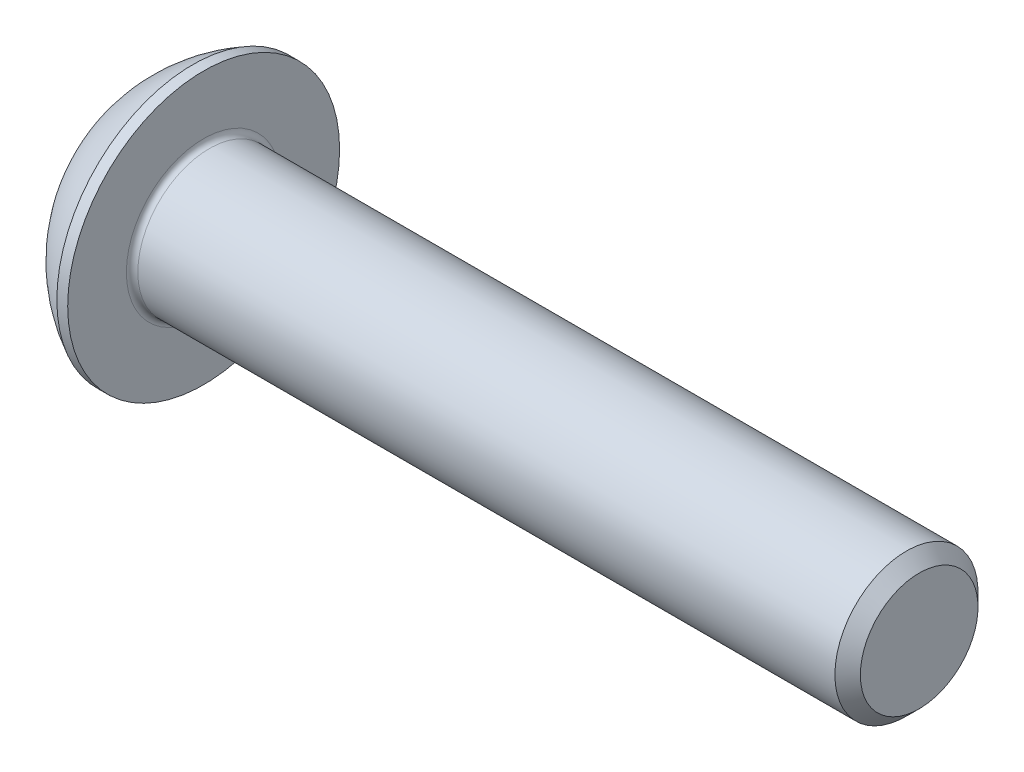
SolidWorks part; units mm, degrees
ref_plane "Plane1" through (0, 0, 0) normal (0, 0, 1) x (1, 0, 0)
ref_plane "Plane2" through (0, 0, 0) normal (0, 1, 0) x (1, 0, 0)
ref_plane "Plane3" through (0, 0, 0) normal (1, 0, 0) x (0, 0, -1)
sketch "BodySke" plane through (0, 0, 0) normal (0, 0, 1) x (1, 0, 0)
  line L0 (27.75, 0) -> (27.75, 2.055)
  line L1 (27.305, 2.5) -> (2.75, 2.5)
  line L2 (2.75, 2.5) -> (2.75, 4.75)
  line L3 (2.75, 4.75) -> (2.37, 4.75)
  line L4 (0, 0) -> (101.6, 0) construction
  line L5 (2.75, -4.75) -> (2.37, -4.75) construction
  line L6 (55.6768, -2.5) -> (2.75, -2.5) construction
  line L7 (27.75, 0) -> (0, 0)
  line L8 (0, 2.375) -> (0, -2.375) construction
  line L9 (0, 0) -> (0, 2.375)
  line L10 (27.75, 2.055) -> (27.305, 2.5)
  line L11 (27.75, -2.055) -> (27.305, -2.5) construction
  line L12 (3.55, 9.525) -> (3.55, -2.5) construction
  line L13 (2.75, 9.525) -> (2.75, -2.5) construction
  arc A1 (0, 2.375) -> (2.37, 4.75) centre (4.755, 0) cw
  dimension "D1" = 4.75
  dimension "Diameter" = 5
  dimension "Length" = 25
  dimension "Head_dia" = 9.5
  dimension "Head_ht" = 2.75
  dimension "Head_side_ht" = 0.38
  dimension "Minor_dia" = 4.11
  dimension "Body_ch_ang" = 45
  dimension "Advance" = 0.8
  dimension "Thread_nom" = 25
revolve "BaseBody" add sketch "BodySke" angle 360 about L4
cosmetic thread "ThreadCosmetic" [suppressed] parameters "Thread_length"=23.4, "Thread_minor"=4.11
fillet "Fillet1" radius 0.2 1 edges at (2.75, 0, 2.5)
sketch "Sketch2" plane through (0, 0, 0) normal (0, 0, 1) x (1, 0, 0)
  line L0 (0, 1.5) -> (1.56, 1.5)
  line L1 (1.56, 1.5) -> (2.426, 0)
  line L3 (2.426, 0) -> (0, 0)
  line L4 (0, 0) -> (0, 1.5)
  line L5 (0, -1.5) -> (1.56, -1.5) construction
  line L6 (0, 0) -> (47.625, 0) construction
  dimension "D2" = 60
  dimension "PreBroach_depth" = 1.56
  dimension "PreBroach_dia" = 3
revolve "PreBroach" cut sketch "Sketch2" angle 360 about L6
sketch "Sketch3" plane through (0, 0, 0) normal (1, 0, 0) x (0, 0, -1)
  line L0 (-1.5, -0.866) -> (-1.5, 0.866)
  line L1 (-1.5, 0.866) -> (0, 1.7321)
  line L2 (0, 1.7321) -> (1.5, 0.866)
  line L3 (1.5, 0.866) -> (1.5, -0.866)
  line L4 (1.5, -0.866) -> (0, -1.7321)
  line L5 (0, -1.7321) -> (-1.5, -0.866)
  dimension "D1" = 1.5
  dimension "D2" = 1.5
  dimension "D3" = 3
  dimension "Hex_size" = 3
extrude "Hex" cut sketch "Sketch3" along normal blind 1.56
sketch "ThdSchSke" plane through (0, 0, 0) normal (0, 0, 1) x (1, 0, 0)
  line L0 (4.35, -2.055) -> (4.0384, -2.5)
  line L1 (4.35, -2.055) -> (4.6616, -2.5)
  line L2 (4.6616, -2.5) -> (4.6616, -3.125)
  line L3 (-3.175, 0) -> (5.1513, 0) construction
  line L5 (4.6616, -3.125) -> (4.0384, -3.125)
  line L6 (4.0384, -3.125) -> (4.0384, -2.5)
  dimension "Thread_minor" = 4.11
  dimension "Diameter" = 5
  dimension "Start" = 4.35
  dimension "SideAngle" = 55
  dimension "VeeAngle" = 70
  dimension "Overcut" = 6.25
revolve "ThreadSchematic" [suppressed] cut sketch "ThdSchSke" angle 360 about L3
pattern_linear "ThdSchPat" [suppressed]
equation "\"D1@BodySke\" = \"Head_dia@BodySke\" * .5"
equation "\"Thread_minor@ThreadCosmetic\" = \"Minor_dia@BodySke\""
equation "\"D1@Sketch3\" = \"Hex_size@Sketch3\" / 2"
equation "\"D2@Sketch3\" = \"D1@Sketch3\""
equation "\"D3@Sketch3\" = \"Hex_size@Sketch3\""
equation "\"Thread_length@ThreadCosmetic\" = ((sgn( (\"Length@BodySke\" - \"Advance@BodySke\" * 2.0) - \"Thread_nom@BodySke\" )-1)*( (\"Length@BodySke\" - \"Advance@BodySke\" * 2.0) - \"Thread_nom@BodySke\" ))/-2+ \"Thread_nom@BodySke\""
equation "\"Thread_minor@ThdSchSke\" = \"Minor_dia@BodySke\""
equation "\"Diameter@ThdSchSke\" = \"Diameter@BodySke\""
equation "\"Overcut@ThdSchSke\" = \"Diameter@BodySke\" * 1.25"
equation "\"Start@ThdSchSke\" = \"Head_ht@BodySke\" + \"Length@BodySke\" - \"Thread_length@ThreadCosmetic\"  '---Non-countersunk---"
equation "\"Num_threads@ThdSchPat\" = int( \"Thread_length@ThreadCosmetic\" / \"Advance@BodySke\" + 0.999 )  + 1"
equation "\"Advance@ThdSchPat\" = \"Thread_length@ThreadCosmetic\" /  (\"Num_threads@ThdSchPat\" - 1) 'relax it"
equation "\"Num_threads@ThdSchPat\" = \"Num_threads@ThdSchPat\" - sgn( \"Num_threads@ThdSchPat\" - 1) '---chamfered tips only---"
